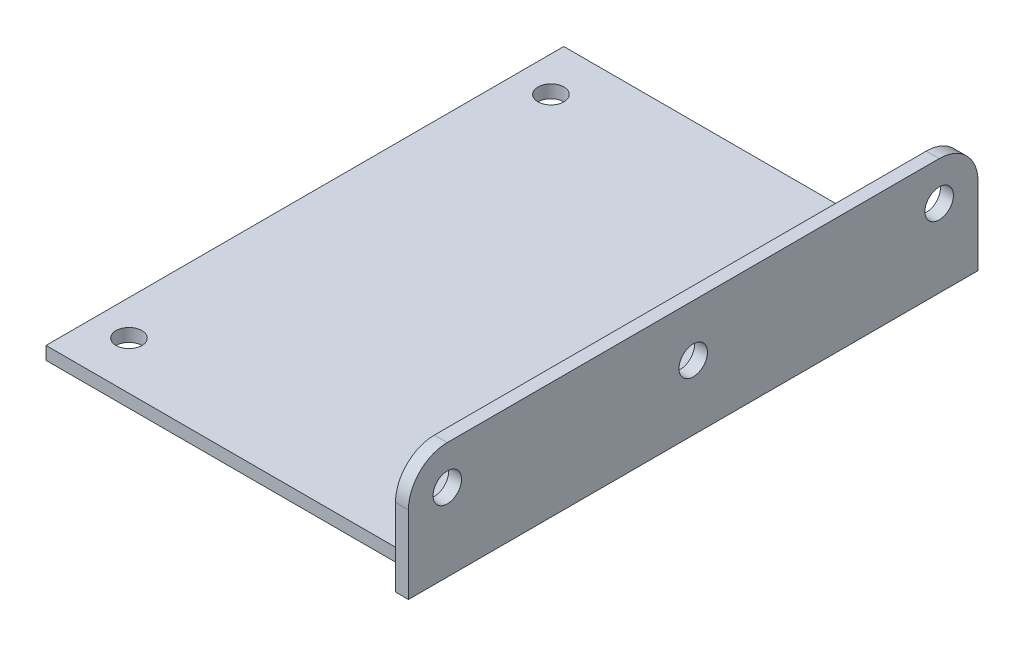
SolidWorks part; units mm, degrees
ref_plane "Front Plane" through (0, 0, 0) normal (0, 0, 1) x (1, 0, 0)
ref_plane "Top Plane" through (0, 0, 0) normal (0, 1, 0) x (1, 0, 0)
ref_plane "Right Plane" through (0, 0, 0) normal (1, 0, 0) x (0, 0, -1)
sketch "Sketch1" plane through (0, 0, 0) normal (0, 1, 0) x (1, 0, 0)
  line L1 (-30, -20) -> (0, -20)
  line L2 (-30, -20) -> (-30, 20)
  line L3 (-30, 20) -> (0, 20)
  line L4 (0, -20) -> (0, 20)
  dimension "D1" = 40
  dimension "D2" = 30
extrude "Boss-Extrude1" add sketch "Sketch1" along normal blind 1
sketch "Sketch4" plane through (0, 0, 0) normal (0, 1, 0) x (1, 0, 0)
  line L0 (-1, 22) -> (-1, -22)
  line L3 (-1, -22) -> (0, -22)
  line L4 (0, -22) -> (0, 22)
  line L5 (0, 22) -> (-1, 22)
  line L6 (0, 0) -> (-9.8037, 0) construction
  line L7 (0, -20) -> (0, 20) construction
  dimension "D1" = 1
  dimension "D2" = 44
extrude "Boss-Extrude2" add sketch "Sketch4" along normal blind 9
sketch "Sketch5" plane through (0, 0, 0) normal (1, 0, 0) x (0, 0, -1)
  line L0 (0, 0) -> (0, 15.2964) construction
  circle A0 centre (-19, 6) radius 1.1
  circle A1 centre (19, 6) radius 1.1
  circle A2 centre (0, 5) radius 1.1
  point P7 (0, 0)
  point P8 (0, 0)
  point P11 (0, 4.1829)
  dimension "D2" = 2.2
  dimension "D1" = 38
  dimension "D3" = 6
  dimension "D4" = 5
extrude "Cut-Extrude1" cut sketch "Sketch5" against normal blind 1
sketch "Sketch7" plane through (0, 0, 0) normal (0, -1, 0) x (1, 0, 0)
  line L0 (0, 0) -> (-36.7236, 0) construction
  point P0 (-27.29, 16.3)
  point P1 (-27.29, -16.3)
  point P5 (0, 0)
  dimension "D1" = 32.6
  dimension "D2" = 27.29
hole_wizard "Ø2.0mm Dowel Hole1" positions "Sketch8" profile "Sketch9" hole size "Ø2.0" standard "ANSI Metric"
sketch "Sketch8" plane through (0, 0, 0) normal (0, -1, 0) x (-1, 0, 0)
  point P0 (27.29, -16.3)
  point P3 (27.29, 16.3)
sketch "Sketch9" plane through (-27.29, 0, 16.3) normal (1, 0, 0) x (0, 0, -1)
  line L0 (0, 0) -> (0, 3.2009)
  line L1 (0, 3.2009) -> (1, 2.6)
  line L2 (1, 2.6) -> (1, 0)
  line L5 (1, 0) -> (0, 0)
  line L10 (0, 3.2009) -> (-1, 2.6) construction
  line L11 (0, -6.35) -> (0, 107.95) construction
  dimension "Hole Dia." = 2
  dimension "Hole Depth" = 2.6
  dimension "Drill Angle" = 118
fillet "Fillet3" radius 3 2 edges at (-0.5, 9, -22) (-0.5, 9, 22)
equation "\"D2@Sketch7\"=54.58/2"
